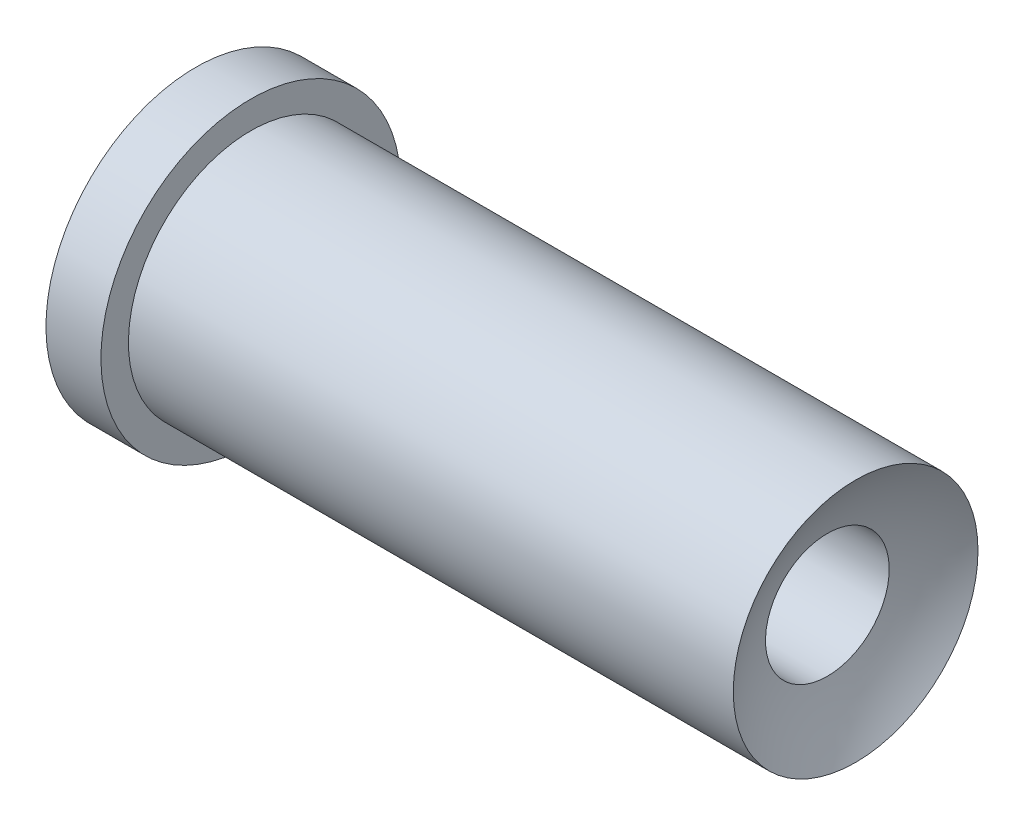
SolidWorks part; units mm, degrees
ref_plane "Front Plane" through (0, 0, 0) normal (0, 0, 1) x (1, 0, 0)
ref_plane "Top Plane" through (0, 0, 0) normal (0, 1, 0) x (1, 0, 0)
ref_plane "Right Plane" through (0, 0, 0) normal (1, 0, 0) x (0, 0, -1)
sketch "Sketch1" plane through (0, 0, 0) normal (0, 0, 1) x (1, 0, 0)
  line L0 (-120, 0) -> (120, 0)
  line L1 (120, 0) -> (120, 44.5)
  line L2 (120, 44.5) -> (-100, 44.5)
  line L3 (-100, 44.5) -> (-100, 54.5)
  line L4 (-100, 54.5) -> (-120, 54.5)
  line L5 (-120, 54.5) -> (-120, 0)
  point P3 (0, 0)
  dimension "D1" = 44.5
  dimension "D2" = 54.5
  dimension "D3" = 20
  dimension "D4" = 240
revolve "Revolve1" add sketch "Sketch1" angle 360 about L0
sketch "Sketch2" plane through (0, 0, 0) normal (0, 0, 1) x (1, 0, 0)
  line L0 (-120, 0) -> (120, 0) construction
  line L2 (66.4812, 0) -> (266.4812, 0)
  line L4 (66.4812, 0) -> (66.4812, 22.5)
  line L5 (66.4812, 22.5) -> (109.7104, 22.5)
  arc A0 (109.7104, 22.5) -> (266.4812, 0) centre (186.4812, 0) cw
  dimension "D1" = 80
  dimension "D2" = 22.5
  dimension "D3" = 120
revolve "Cut-Revolve2" cut sketch "Sketch2" angle 360 about L2
